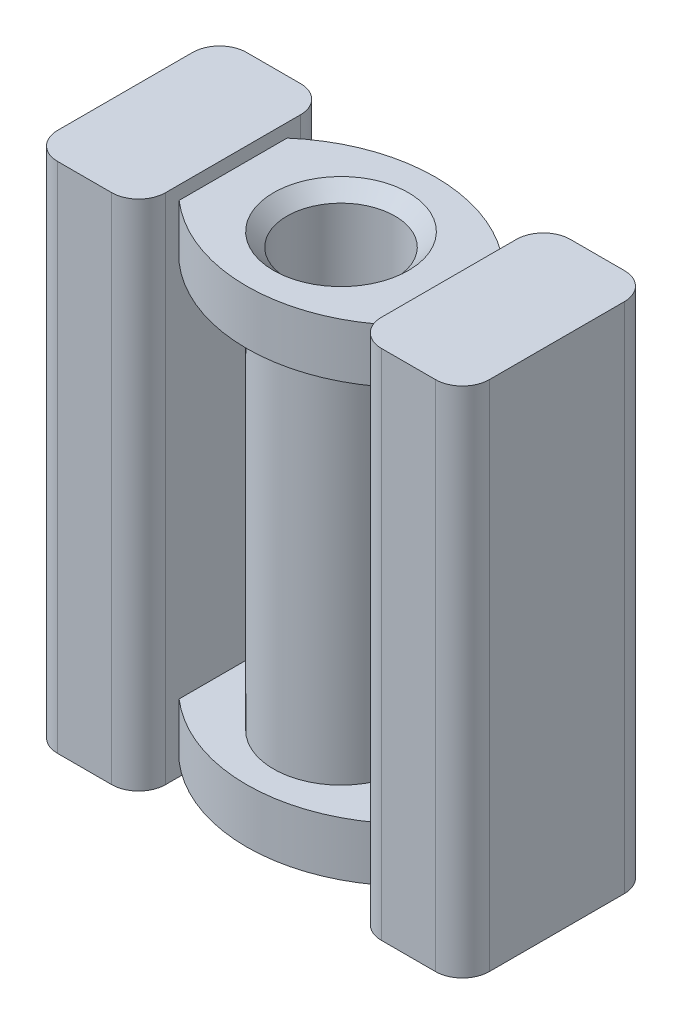
SolidWorks part; units mm, degrees
material "PBT General Purpose"
ref_plane "Front Plane" through (0, 0, 0) normal (0, 0, 1) x (1, 0, 0)
ref_plane "Top Plane" through (0, 0, 0) normal (0, 1, 0) x (1, 0, 0)
ref_plane "Right Plane" through (0, 0, 0) normal (1, 0, 0) x (0, 0, -1)
sketch "Sketch1" plane through (0, 0, 0) normal (0, 1, 0) x (1, 0, 0)
  circle A0 centre (0, 0) radius 1.25
  dimension "D1" = 2.5
extrude "Boss-Extrude1" add sketch "Sketch1" along normal mid plane 9
sketch "Sketch2" plane through (0, 0, 0) normal (0, 1, 0) x (1, 0, 0)
  line L0 (-2, -1) -> (-2, 1)
  line L2 (0.8408, 1.75) -> (-0.8408, 1.75) construction
  line L3 (0.8773, -1.75) -> (-0.8773, -1.75) construction
  line L4 (2, -1) -> (2, 1)
  line L5 (0, -1.75) -> (0, 1.75) construction
  line L6 (-2, 0) -> (2, 0) construction
  arc A0 (-2, 1) -> (2, 1) centre (0, -1.2917) cw
  arc A1 (-2, -1) -> (2, -1) centre (0, 1.2917) ccw
  point P3 (-2, 0)
  point P13 (0, 1.75)
  point P15 (0, -1.75)
  point P19 (0, 0)
  point P28 (0, 0)
  dimension "D1" = 2
  dimension "D2" = 3.5
  dimension "D3" = 2
extrude "Boss-Extrude2" add sketch "Sketch2" against normal blind 1 from offset 3.5 offset against normal yes
mirror "Mirror2" about plane through (0, 0, 0) normal (0, 1, 0) of "Boss-Extrude2"
sketch "Sketch3" plane through (0, 0, 0) normal (0, 1, 0) x (1, 0, 0)
  line L0 (-2, 1) -> (-2, -1) construction
  line L1 (-4, 1.75) -> (-2, 1.75)
  line L2 (-4, 1.75) -> (-4, -1.75)
  line L3 (-4, -1.75) -> (-2, -1.75)
  line L4 (-2, 1.75) -> (-2, -1.75)
  arc A0 (2, 1) -> (-2, 1) centre (0, -1.2917) ccw construction
  arc A1 (-2, -1) -> (2, -1) centre (0, 1.2917) ccw construction
  dimension "D1" = 2
extrude "Boss-Extrude3" add sketch "Sketch3" along normal mid plane 9.5
mirror "Mirror3" about plane through (0, 0, 0) normal (1, 0, 0) of "Boss-Extrude3"
fillet "Fillet2" radius 0.5 8 edges at (4, 0, 1.75) (2, 0, 1.75) (-2, 0, 1.75) (-4, 0, 1.75) (-2, 0, -1.75) (-4, 0, -1.75) (2, 0, -1.75) (4, 0, -1.75)
sketch "Sketch6" plane through (0, 4.5, 0) normal (0, 1, 0) x (1, 0, 0)
  point P0 (0, 0)
hole_wizard "Ø2.0mm Dowel Hole1" positions "Sketch6" profile "Sketch5" hole size "Ø2.0" standard "ANSI Metric" end condition through all
sketch "Sketch5" plane through (0, 4.5, 0) normal (1, 0, 0) x (0, 0, 1)
  line L0 (0, 0) -> (0, 9.25)
  line L1 (0, 9.25) -> (1, 9.25)
  line L2 (1, 9.25) -> (1, 0)
  line L5 (1, 0) -> (0, 0)
  line L11 (0, -6.35) -> (0, 107.95) construction
  dimension "Thru Hole Dia." = 2
  dimension "Thru Hole Depth" = 9.25
chamfer "Chamfer1" distance 0.25 angle 45 2 edges at (0, -4.5, 1) (0, 4.5, 1)
